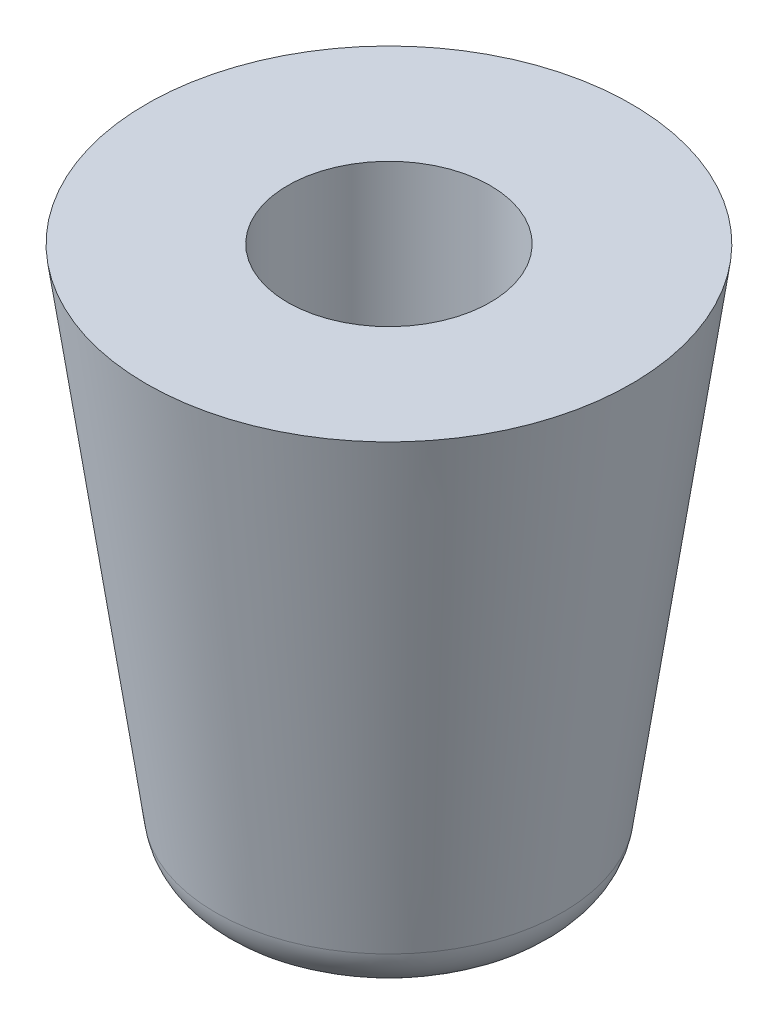
SolidWorks part; units mm, degrees
ref_plane "Front Plane" through (0, 0, 0) normal (0, 0, 1) x (1, 0, 0)
ref_plane "Top Plane" through (0, 0, 0) normal (0, 1, 0) x (1, 0, 0)
ref_plane "Right Plane" through (0, 0, 0) normal (1, 0, 0) x (0, 0, -1)
sketch "Sketch1" plane through (0, 0, 0) normal (0, 1, 0) x (1, 0, 0)
  circle A0 centre (0, 0) radius 5.715
  dimension "D1" = 11.43
extrude "Boss-Extrude1" add sketch "Sketch1" against normal blind 12.7 draft 8
sketch "Sketch2" plane through (0, 0, 0) normal (0, 1, 0) x (1, 0, 0)
  circle A0 centre (0, 0) radius 2.3876
  dimension "D1" = 4.7752
extrude "Cut-Extrude1" cut sketch "Sketch2" against normal blind 10 contours A0
fillet "Fillet1" radius 1.27 1 edges at (0, -12.7, 3.9301)
